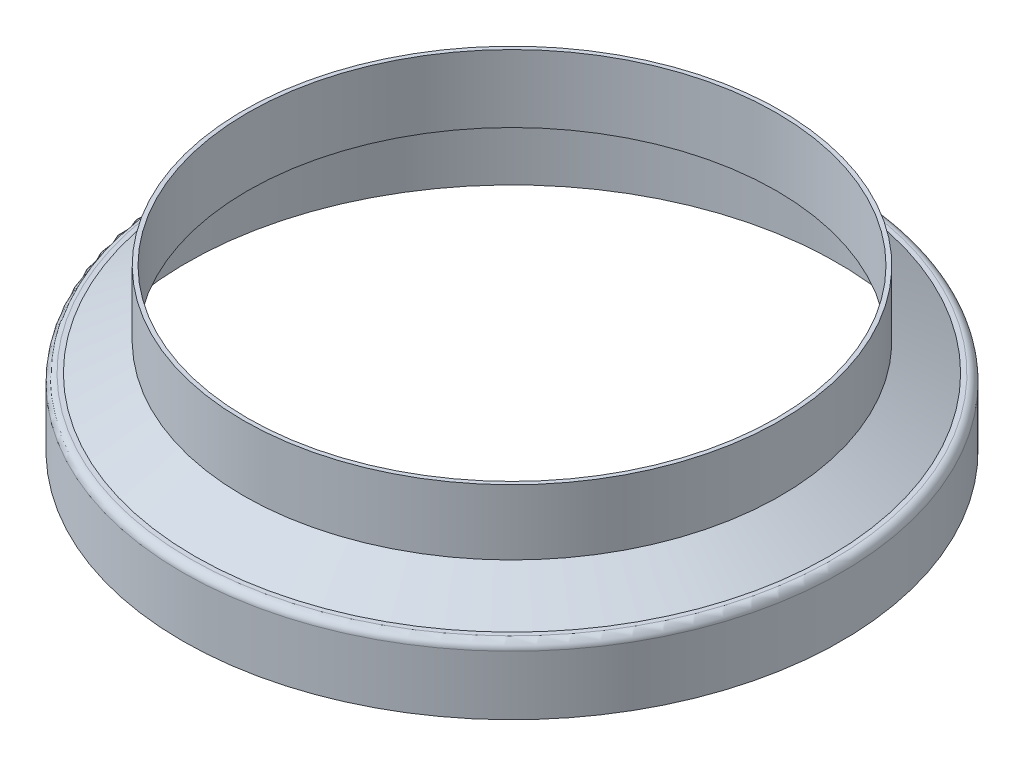
SolidWorks part; units mm, degrees
ref_plane "Front Plane" through (0, 0, 0) normal (0, 0, 1) x (1, 0, 0)
ref_plane "Top Plane" through (0, 0, 0) normal (0, 1, 0) x (1, 0, 0)
ref_plane "Right Plane" through (0, 0, 0) normal (1, 0, 0) x (0, 0, -1)
ref_plane "Plane1" through (0, 0, 0) normal (0, 0, -1) x (-1, 0, 0)
sketch "Sketch1" plane through (0, 0, 0) normal (0, 0, -1) x (-1, 0, 0)
  line L0 (-21.5265, 8.1026) -> (-18.0086, 10.1337)
  line L1 (-18.0086, 10.1337) -> (-18.0086, 14.732)
  line L2 (-18.0086, 14.732) -> (-18.288, 14.732)
  line L3 (-18.288, 14.732) -> (-18.288, 10.295)
  line L4 (-18.288, 10.295) -> (-21.6014, 8.382)
  line L5 (-21.6014, 8.382) -> (-21.9075, 8.382)
  line L6 (-22.4409, 7.8486) -> (-22.4409, 3.81)
  line L7 (-22.4409, 3.81) -> (-22.1615, 3.81)
  line L8 (-22.1615, 3.81) -> (-22.1615, 7.8486)
  line L9 (-21.9075, 8.1026) -> (-21.5265, 8.1026)
  line L10 (0, 3.81) -> (0, 14.732) construction
  arc A0 (-21.9075, 8.382) -> (-22.4409, 7.8486) centre (-21.9075, 7.8486) ccw
  arc A1 (-22.1615, 7.8486) -> (-21.9075, 8.1026) centre (-21.9075, 7.8486) cw
revolve "Revolve1" add sketch "Sketch1" angle 360 about L10
